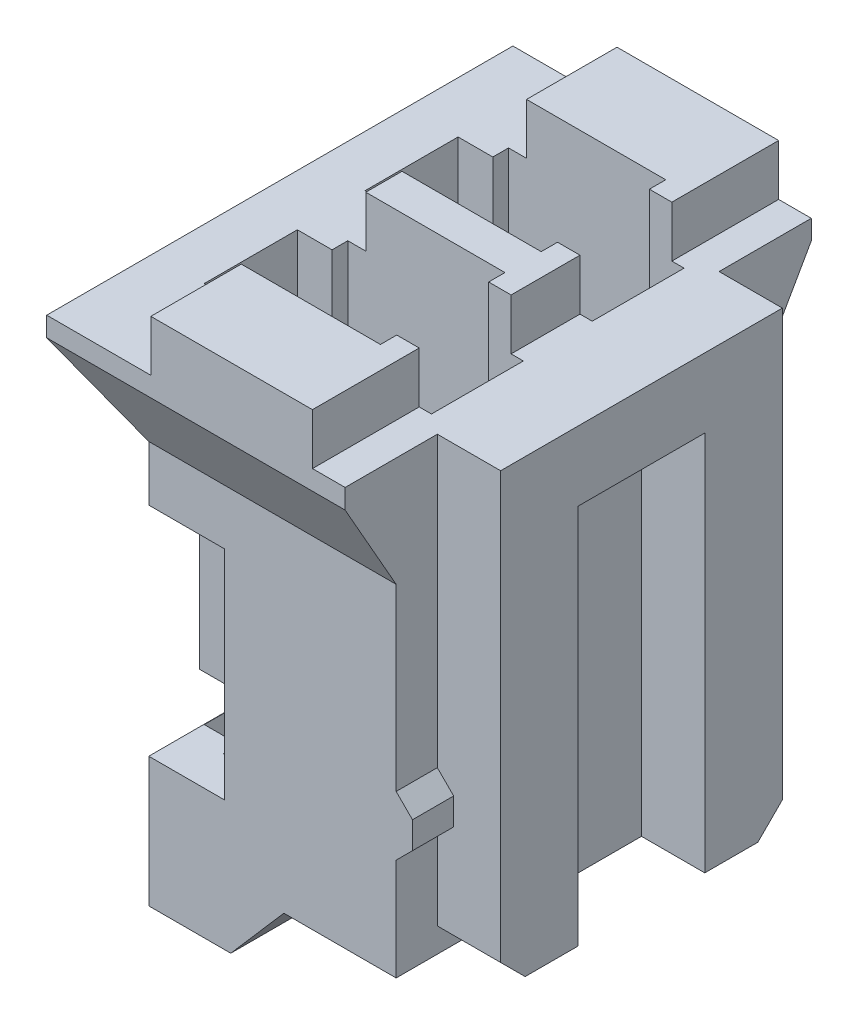
SolidWorks part; units mm, degrees
ref_plane "YZ" through (0, 0, 0) normal (0, 0, 1) x (1, 0, 0)
ref_plane "XY" through (0, 0, 0) normal (0, 1, 0) x (1, 0, 0)
ref_plane "XZ" through (0, 0, 0) normal (1, 0, 0) x (0, 0, -1)
sketch "Sketch1" plane through (0, 0, 0) normal (0, 1, 0) x (1, 0, 0)
  line L0 (2.25, -2.9) -> (-2.25, 2.9) construction
  line L1 (-2.25, -2.9) -> (2.25, -2.9)
  line L2 (-2.25, -2.9) -> (-2.25, 2.9)
  line L3 (-2.25, 2.9) -> (2.25, 2.9)
  line L4 (2.25, -2.9) -> (2.25, 2.9)
  dimension "Length" = 5.8
  dimension "D2" = 4.5
extrude "Extrude1" add sketch "Sketch1" along normal blind 7
sketch "Sketch10" plane through (0, 4.9, 2.9) normal (0, 0, -1) x (1, 0, 0)
  line L0 (-0.5948, 4.9) -> (0.0656, 4.138)
  line L2 (-2.25, 4.9) -> (2.25, 4.9) construction
  line L4 (0.0656, 4.138) -> (2.25, 4.138)
  line L5 (2.25, -2.1) -> (2.25, 4.9) construction
  line L6 (2.25, 4.138) -> (2.25, 4.9)
  line L7 (2.25, 4.9) -> (-0.5948, 4.9)
  line L8 (-2.25, -1.2214) -> (-1.615, -0.1038)
  line L9 (-2.25, -2.1) -> (-2.25, 4.9) construction
  line L10 (-1.615, -0.1038) -> (-1.615, 4.9)
  line L11 (-1.615, 4.9) -> (-2.25, 4.9)
  line L12 (-2.25, 4.9) -> (-2.25, -1.2214)
  line L14 (-2.25, -2.1) -> (-0.9546, -2.1)
  line L15 (-2.25, -2.1) -> (-2.25, -1.465)
  line L16 (-2.25, -1.465) -> (-0.9546, -1.465)
  line L17 (-0.9546, -2.1) -> (-0.9546, -1.465)
  line L18 (1.0562, -2.1) -> (2.25, -2.1)
  line L19 (1.0562, -2.1) -> (1.0562, -1.465)
  line L20 (1.0562, -1.465) -> (2.25, -1.465)
  line L21 (2.25, -2.1) -> (2.25, -1.465)
  line L22 (-2.25, -2.1) -> (2.25, -2.1) construction
  dimension "D1" = 2.8448
  dimension "D2" = 0.762
  dimension "D3" = 2.1844
  dimension "D4" = 0.635
  dimension "D5" = 5.0038
  dimension "D6" = 6.1214
  dimension "D7" = 1.1938
  dimension "D8" = 1.2954
extrude "Cut-Extrude7" cut sketch "Sketch10" along normal through all
sketch "Sketch17" plane through (2.25, 0, 0) normal (1, 0, 0) x (0, 0, -1)
  line L0 (0, 0) -> (0, 7.2285) construction
  line L2 (-2.9, 5.0038) -> (-2.9, 0) construction
  line L3 (-2.9, 0) -> (-2.265, 0)
  line L5 (-2.9, 5.0038) -> (-2.9, 0) construction
  line L6 (-2.9, 0) -> (-2.9, 6.1214) construction
  line L7 (-2.9, 0) -> (-2.9, 6.1214)
  line L8 (-2.265, 0) -> (-2.265, 5.0038)
  line L9 (-2.265, 5.0038) -> (-2.9, 6.1214)
  line L10 (-2.9, 5.0038) -> (-2.265, 5.0038) construction
  line L11 (2.9, 0) -> (2.265, 0)
  line L12 (2.265, 0) -> (2.265, 5.0038)
  line L13 (2.9, 0) -> (2.9, 6.1214)
  line L14 (2.265, 5.0038) -> (2.9, 6.1214)
extrude "Cut-Extrude13" cut sketch "Sketch17" against normal through all
sketch "Sketch3" plane through (0, 0.762, 0) normal (0, -1, 0) x (1, 0, 0)
  line L1 (0.0656, -2.265) -> (0.0656, 2.265) construction
  line L5 (1.2324, 1.5334) -> (1.2324, 0.4666)
  line L6 (0.1656, 0.4666) -> (1.2324, 0.4666)
  line L7 (0.1656, 1.5334) -> (0.1656, 0.4666)
  line L8 (0.1656, 1.5334) -> (1.2324, 1.5334)
  line L9 (1.2324, 1) -> (0.1656, 1) construction
  line L10 (-2.25, 2.9) -> (2.25, 2.9) construction
  dimension "D1" = 1.0668
  dimension "D2" = 0.1
  dimension "D3" = 1.9
extrude "Mating Side Chamfers" cut sketch "Sketch3" against normal blind 0.508 draft 45
sketch "Sketch18" plane through (2.25, 0, 0) normal (1, 0, 0) x (0, 0, -1)
  line L0 (0, 0) -> (0, 7.2764) construction
  line L1 (2.265, 0.762) -> (-2.265, 0.762) construction
  line L2 (0.7874, 0.762) -> (0.7874, 5.5014)
  line L3 (-0.7874, 0.762) -> (-0.7874, 5.5014)
  line L4 (-0.7874, 5.5014) -> (0.7874, 5.5014)
  line L5 (-1.7526, 1.0668) -> (-1.7526, 6.365)
  line L6 (0.7874, 0.762) -> (1.4478, 0.762)
  line L7 (1.4478, 0.762) -> (1.7526, 1.0668)
  line L8 (1.7526, 1.0668) -> (1.7526, 6.365)
  line L9 (2.9, 6.365) -> (-2.9, 6.365) construction
  line L10 (1.7526, 6.365) -> (-1.7526, 6.365)
  line L11 (-1.4478, 0.762) -> (-1.7526, 1.0668)
  line L12 (-0.7874, 0.762) -> (-1.4478, 0.762)
  line L13 (2.9, 6.365) -> (2.9, 7) construction
  line L14 (2.9, 7) -> (-2.9, 7) construction
  line L15 (-2.9, 6.365) -> (-2.9, 7) construction
  line L16 (2.9, 0) -> (2.9, 7)
  line L17 (2.9, 7) -> (-2.9, 7)
  line L18 (-2.9, 0) -> (-2.9, 7)
  line L19 (2.265, 0) -> (-2.265, 0) construction
  line L20 (2.9, 0) -> (-2.9, 0)
  dimension "D1" = 0.9652
  dimension "D2" = 225
  dimension "D3" = 0.8636
  dimension "D4" = 0.6604
  dimension "D5" = 1.5748
extrude "Polarizing Keyway" cut sketch "Sketch18" against normal blind 0.7874
sketch "Sketch4" plane through (0, 0, 0) normal (0, -1, 0) x (1, 0, 0)
  line L8 (0.2656, 0.5666) -> (1.1324, 0.5666)
  line L9 (1.1324, 0.5666) -> (1.1324, 1.4334)
  line L10 (1.1324, 1.4334) -> (0.2656, 1.4334)
  line L11 (0.2656, 1.4334) -> (0.2656, 0.5666)
  line L12 (0.2656, 0.5666) -> (1.1324, 0.5666)
  line L13 (1.1324, 0.5666) -> (1.1324, 1.4334)
  line L14 (1.1324, 1.4334) -> (0.2656, 1.4334)
  line L15 (0.2656, 1.4334) -> (0.2656, 0.5666)
  dimension "D1" = 0.1
extrude "Terminal Holes" cut sketch "Sketch4" against normal through all
sketch "Sketch14" plane through (0, 7, 0) normal (0, 1, 0) x (-1, 0, 0)
  line L0 (1.6108, 0.2253) -> (1.6108, 1.7747) construction
  line L1 (-1.2086, 0.2253) -> (-1.2086, 1.7747) construction
  line L4 (1.6108, 0.4207) -> (1.6108, 1.5793)
  line L8 (-1.1324, 0.5666) -> (-1.1324, 1.4334) construction
  line L9 (-1.1324, 1.4334) -> (-0.2656, 1.4334) construction
  line L10 (-0.2656, 0.5666) -> (-1.1324, 0.5666) construction
  line L11 (-0.2656, 1.4334) -> (-0.2656, 0.5666) construction
  line L12 (-1.1324, 0.5666) -> (-1.1324, 1.4334)
  line L13 (-1.1324, 1.4334) -> (-0.2656, 1.4334)
  line L14 (-0.2656, 0.5666) -> (-1.1324, 0.5666)
  line L15 (-0.2656, 1.4334) -> (-0.2656, 0.5666)
  line L26 (0.2011, 0.2253) -> (0.2011, 1.7747) construction
  line L27 (1.6108, 0.2253) -> (-1.2086, 0.2253) construction
  line L29 (1.6108, 1.7747) -> (-1.2086, 1.7747) construction
  line L42 (-1.1324, 1) -> (-1.2086, 1) construction
  line L43 (1.179, 0.2253) -> (-0.7768, 0.2253)
  line L44 (-0.7768, 0.2253) -> (-0.7768, 0.4285)
  line L45 (-0.7768, 0.4285) -> (-1.2086, 0.4285)
  line L46 (-1.2086, 0.4285) -> (-1.2086, 1)
  line L47 (-1.2086, 1.5715) -> (-1.2086, 1)
  line L48 (-0.7768, 1.5715) -> (-1.2086, 1.5715)
  line L49 (-0.7768, 1.7747) -> (-0.7768, 1.5715)
  line L51 (-0.7768, 1.7747) -> (1.179, 1.7747)
  line L52 (1.179, 1.7747) -> (1.179, 1.5793)
  line L53 (1.179, 1.5793) -> (1.6108, 1.5793)
  line L56 (1.179, 0.4207) -> (1.6108, 0.4207)
  line L57 (1.179, 0.2253) -> (1.179, 0.4207)
  line L58 (-2.25, -1.7526) -> (-2.25, 1.7526) construction
  dimension "D2" = 0.4318
  dimension "D3" = 1.1585
  dimension "D4" = 1.5494
  dimension "D1" = 1.0414
  dimension "D5" = 0.2032
  dimension "D6" = 2.8194
extrude "Terminal Cutout" cut sketch "Sketch14" against normal offset from surface (5.73 mm away) 0.508 up to face at (1.4922, 0.762, 0)
sketch "Sketch19" plane through (-1.615, 0, 0) normal (-1, 0, 0) x (0, 0, 1)
  line L0 (0.2253, 7) -> (1.7747, 7) construction
  line L1 (0.2253, 7) -> (1.7747, 7) construction
  line L2 (0.365, 4.318) -> (-0.016, 4.318) construction
  line L3 (-0.016, 4.318) -> (-0.016, 0) construction
  line L4 (0.365, 4.318) -> (0.365, 2.2352)
  line L5 (0.365, 2.2352) -> (1.635, 2.2352)
  line L6 (1.635, 4.318) -> (1.635, 2.2352)
  line L7 (0.365, 4.318) -> (-0.016, 4.318)
  line L8 (1, 7) -> (1, 2.2352) construction
  line L9 (-0.016, 4.318) -> (-0.016, 1.6129)
  line L10 (-0.016, 1.6129) -> (0.7079, 1.6129)
  line L11 (0.7079, 1.6129) -> (0.7079, 0.5842)
  line L12 (-2.265, 0) -> (2.265, 0) construction
  line L13 (-2.265, 5.0038) -> (2.265, 5.0038) construction
  line L14 (1.2921, 1.6129) -> (1.2921, 0.5842)
  line L15 (0.7079, 0.5842) -> (1.2921, 0.5842)
  line L16 (1.635, 4.318) -> (2.016, 4.318)
  line L17 (2.016, 1.6129) -> (1.2921, 1.6129)
  line L18 (2.016, 4.318) -> (2.016, 1.6129)
  dimension "D1" = 0.762
  dimension "D2" = 1.27
  dimension "D3" = 0.6858
  dimension "D4" = 2.2352
  dimension "D5" = 1.6129
  dimension "D6" = 0.5842
  dimension "D7" = 0.5842
sketch "Sketch11" plane through (0, 0, 2.265) normal (0, 0, 1) x (1, 0, 0)
  line L0 (0.0656, 0.762) -> (1.4626, 0.762) construction
  line L1 (1.4626, 2.772) -> (1.4626, 2.032)
  line L2 (1.4626, 2.402) -> (1.6658, 2.402) construction
  line L5 (1.4626, 2.772) -> (1.6658, 2.5688)
  line L6 (1.4626, 2.032) -> (1.6658, 2.2352)
  line L7 (1.6658, 2.5688) -> (1.6658, 2.2352)
  line L9 (1.4626, 0.762) -> (1.4626, 5.0038) construction
  dimension "D1" = 45
  dimension "D2" = 0.2032
  dimension "D3" = 0.3336
  dimension "D4" = 1.27
extrude "Ramp1" add sketch "Sketch11" against normal blind 0.7874
extrude "TerminalLock Cutout" cut sketch "Sketch19" against normal blind 0.9398
sketch "Sketch20" plane through (-1.615, 0, 0) normal (-1, 0, 0) x (0, 0, 1)
  line L0 (2.265, 5.0038) -> (2.265, 0) construction
  line L1 (2.016, 1.6129) -> (2.016, 4.318) construction
  line L2 (2.265, 4.318) -> (2.265, 1.6129)
  line L3 (2.016, 1.6129) -> (2.016, 4.318)
  line L4 (2.016, 4.318) -> (2.265, 4.318)
  line L5 (2.016, 1.6129) -> (2.265, 1.6129)
  line L6 (0, 0) -> (0, 7.2562) construction
  line L7 (-2.016, 1.6129) -> (-2.265, 1.6129)
  line L8 (-2.265, 4.318) -> (-2.265, 1.6129)
  line L9 (-2.016, 4.318) -> (-2.265, 4.318)
  line L10 (-2.016, 1.6129) -> (-2.016, 4.318)
extrude "Cut-Extrude16" cut sketch "Sketch20" against normal up to vertex (0.9398 mm away) up to point (-0.6752, 1.6129, 2.016)
pattern_linear "LPattern2" count 2 spacing 2 along (0, 0, 1) of "Terminal Holes", "Mating Side Chamfers", "Terminal Cutout", "TerminalLock Cutout"
mirror "Mirror1" about plane through (0, 0, 0) normal (0, 0, 1) of "Ramp1"
